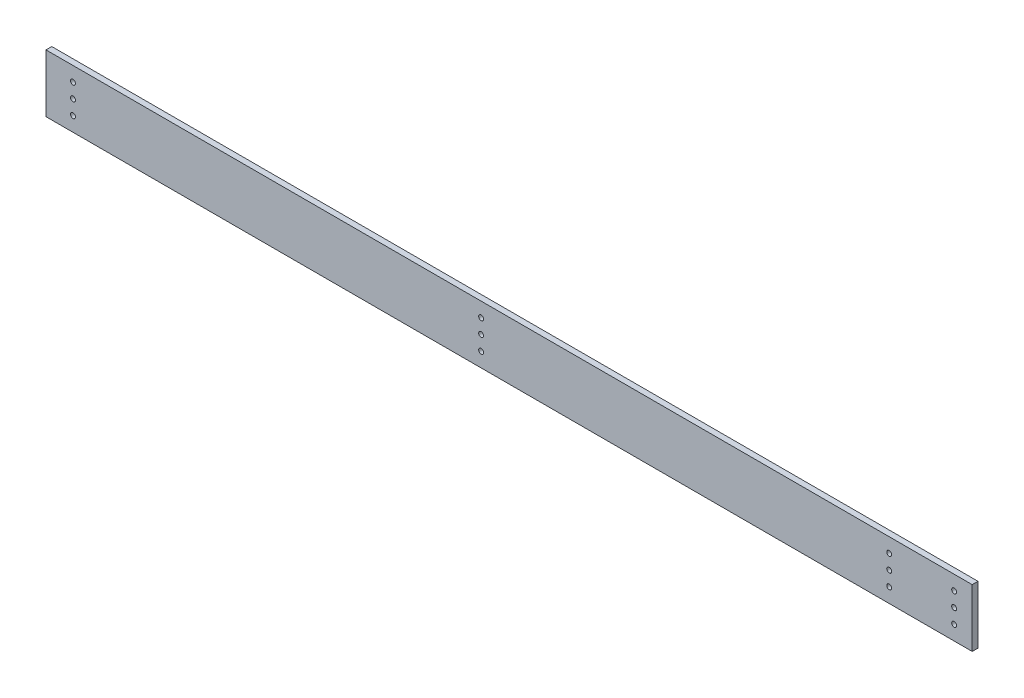
SolidWorks part; units mm, degrees
material "6061 Alloy"
ref_plane "Front Plane" through (0, 0, 0) normal (0, 0, 1) x (1, 0, 0)
ref_plane "Top Plane" through (0, 0, 0) normal (0, 1, 0) x (1, 0, 0)
ref_plane "Right Plane" through (0, 0, 0) normal (1, 0, 0) x (0, 0, -1)
sketch "Sketch1" plane through (0, 0, 0) normal (0, 0, 1) x (1, 0, 0)
  line L1 (0, 0) -> (508, 0)
  line L2 (0, 0) -> (0, 31.75)
  line L3 (0, 31.75) -> (508, 31.75)
  line L4 (508, 0) -> (508, 31.75)
  dimension "D1" = 31.75
  dimension "D2" = 508
extrude "Boss-Extrude1" add sketch "Sketch1" along normal blind 3.175
sketch "Sketch2" plane through (0, 0, 3.175) normal (0, 0, 1) x (1, 0, 0)
  line L0 (0, 15.875) -> (508, 15.875) construction
  line L1 (0, 31.75) -> (0, 0) construction
  line L2 (508, 0) -> (508, 31.75) construction
  circle A0 centre (14.8082, 23.8252) radius 1.3589
  circle A1 centre (14.8082, 15.875) radius 1.3589
  circle A2 centre (14.8082, 7.9248) radius 1.3589
  circle A3 centre (462.4832, 23.8252) radius 1.3589
  circle A4 centre (462.4832, 15.875) radius 1.3589
  circle A5 centre (462.4832, 7.9248) radius 1.3589
  circle A6 centre (498.094, 23.8252) radius 1.3589
  circle A7 centre (498.094, 15.875) radius 1.3589
  circle A8 centre (498.094, 7.9248) radius 1.3589
  circle A9 centre (238.6584, 23.8252) radius 1.3589
  circle A10 centre (238.6584, 15.875) radius 1.3589
  circle A11 centre (238.6584, 7.9248) radius 1.3589
  dimension "D1" = 2.7178
  dimension "D2" = 14.8082
  dimension "D3" = 7.9502
  dimension "D4" = 3
extrude "Cut-Extrude1" cut sketch "Sketch2" against normal through all
